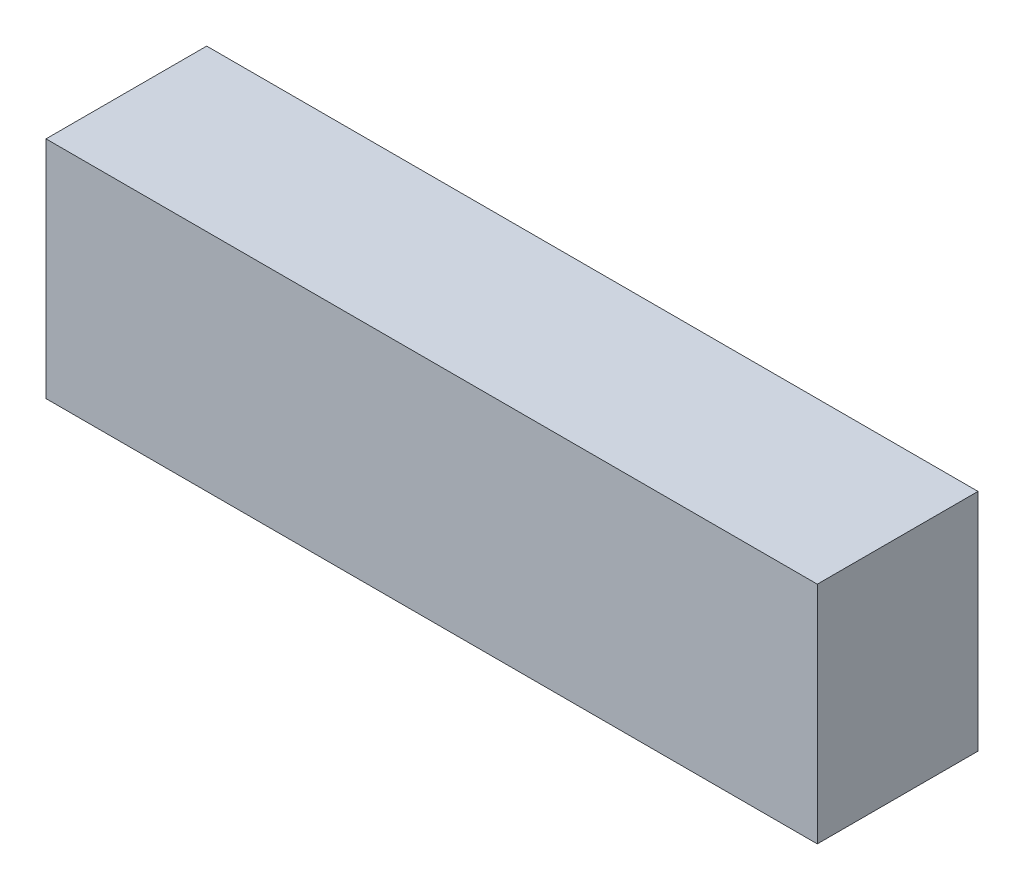
SolidWorks part; units mm, degrees
ref_plane "Front Plane" through (0, 0, 0) normal (0, 0, 1) x (1, 0, 0)
ref_plane "Top Plane" through (0, 0, 0) normal (0, 1, 0) x (1, 0, 0)
ref_plane "Right Plane" through (0, 0, 0) normal (1, 0, 0) x (0, 0, -1)
sketch "Sketch1" plane through (0, 0, 0) normal (0, 0, 1) x (1, 0, 0)
  line L1 (0, 0) -> (120, 0)
  line L2 (0, 0) -> (0, 35)
  line L3 (0, 35) -> (120, 35)
  line L4 (120, 0) -> (120, 35)
  dimension "D1" = 120
  dimension "D2" = 35
extrude "Boss-Extrude1" add sketch "Sketch1" along normal blind 25
